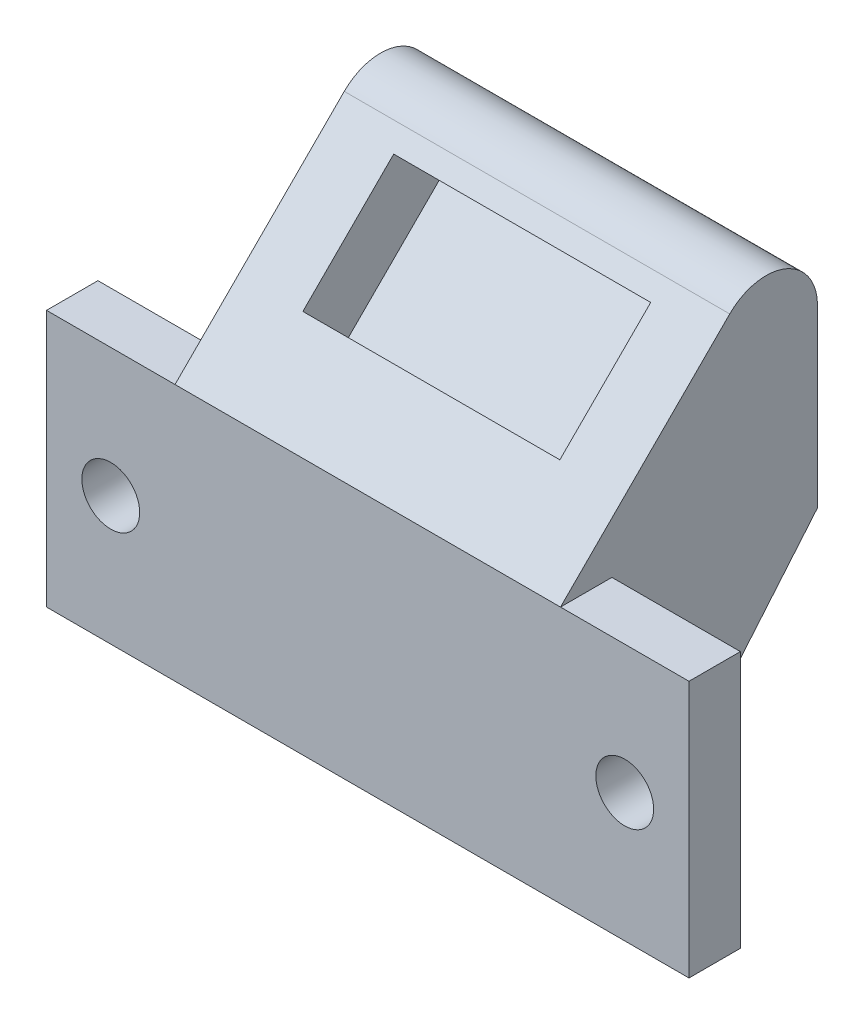
SolidWorks part; units mm, degrees
ref_plane "Front Plane" through (0, 0, 0) normal (0, 0, 1) x (1, 0, 0)
ref_plane "Top Plane" through (0, 0, 0) normal (0, 1, 0) x (1, 0, 0)
ref_plane "Right Plane" through (0, 0, 0) normal (1, 0, 0) x (0, 0, -1)
sketch "Sketch1" plane through (0, 0, 0) normal (1, 0, 0) x (0, 0, -1)
  line L0 (0, 20) -> (20, 40)
  line L1 (0, 0) -> (20, 0)
  line L2 (0, 0) -> (0, 20)
  line L4 (20, 0) -> (20, 20)
  line L5 (20, 40) -> (20, 20)
  dimension "D1" = 20
extrude "Boss-Extrude1" add sketch "Sketch1" along normal blind 30
sketch "Sketch2" plane through (0, 0, 0) normal (0, 0, 1) x (1, 0, 0)
  line L1 (0, 20) -> (-10, 20)
  line L2 (0, 20) -> (0, 0)
  line L3 (0, 0) -> (-10, 0)
  line L4 (-10, 20) -> (-10, 0)
  line L5 (30, 0) -> (40, 0)
  line L6 (30, 0) -> (30, 20)
  line L7 (30, 20) -> (40, 20)
  line L8 (40, 0) -> (40, 20)
  circle A0 centre (-5, 10) radius 2.25
  circle A1 centre (35, 10) radius 2.25
  point P13 (-5, 20)
  dimension "D3" = 4.5
  dimension "D1" = 10
  dimension "D2" = 10
extrude "Boss-Extrude2" add sketch "Sketch2" against normal blind 4
sketch "Sketch3" plane through (0, 10, 10) normal (0, 0.7071, 0.7071) x (1, 0, 0)
  line L0 (30, 42.4264) -> (0, 42.4264) construction
  line L1 (5, 21.1421) -> (25, 21.1421)
  line L2 (5, 21.1421) -> (5, 31.1421)
  line L3 (5, 31.1421) -> (25, 31.1421)
  line L4 (25, 21.1421) -> (25, 31.1421)
  line L5 (30, 14.1421) -> (0, 14.1421) construction
  point P4 (15, 31.1421)
  point P7 (15, 42.4264)
  dimension "D1" = 20
  dimension "D2" = 10
  dimension "D3" = 7
extrude "Cut-Extrude1" cut sketch "Sketch3" against normal blind 5
fillet "Fillet1" radius 4 1 edges at (15, 40, -20)
chamfer "Chamfer1" distance 14 angle 50 1 edges at (15, 0, -20)
